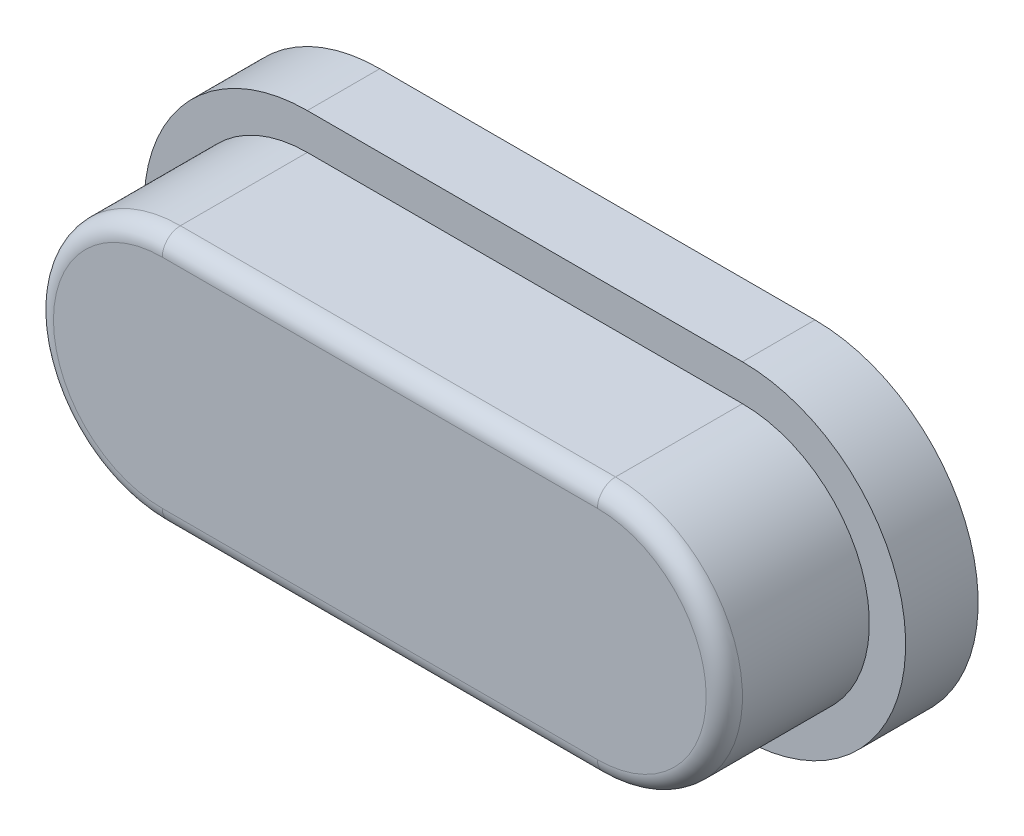
SolidWorks part; units mm, degrees
material "Plastique personnalisé"
ref_plane "Plan de face" through (0, 0, 0) normal (0, 0, 1) x (1, 0, 0)
ref_plane "Plan de dessus" through (0, 0, 0) normal (0, 1, 0) x (1, 0, 0)
ref_plane "Plan de droite" through (0, 0, 0) normal (1, 0, 0) x (0, 0, -1)
sketch "Esquisse1" plane through (0, 0, 0) normal (0, 0, 1) x (1, 0, 0)
  line L0 (-3, 0) -> (3, 0) construction
  line L1 (-3, 1.75) -> (3, 1.75)
  line L2 (-3, -1.75) -> (3, -1.75)
  arc A0 (-3, 1.75) -> (-3, -1.75) centre (-3, 0) ccw
  arc A1 (3, -1.75) -> (3, 1.75) centre (3, 0) ccw
  point P2 (0, 0)
extrude "Boss.-Extru.1" add sketch "Esquisse1" along normal blind 2
sketch "Esquisse3" plane through (0, 0, 0) normal (0, 0, 1) x (1, 0, 0)
  line L0 (-3, 0) -> (3, 0) construction
  line L1 (-3, 2.25) -> (3, 2.25)
  line L2 (-3, -2.25) -> (3, -2.25)
  arc A0 (-3, 2.25) -> (-3, -2.25) centre (-3, 0) ccw
  arc A1 (3, -2.25) -> (3, 2.25) centre (3, 0) ccw
  point P2 (0, 0)
extrude "Boss.-Extru.2" add sketch "Esquisse3" against normal blind 1
fillet "Congé1" radius 0.25 4 edges at (0, -1.75, 2) (-4.75, 0, 2) (0, 1.75, 2) (4.75, 0, 2)
